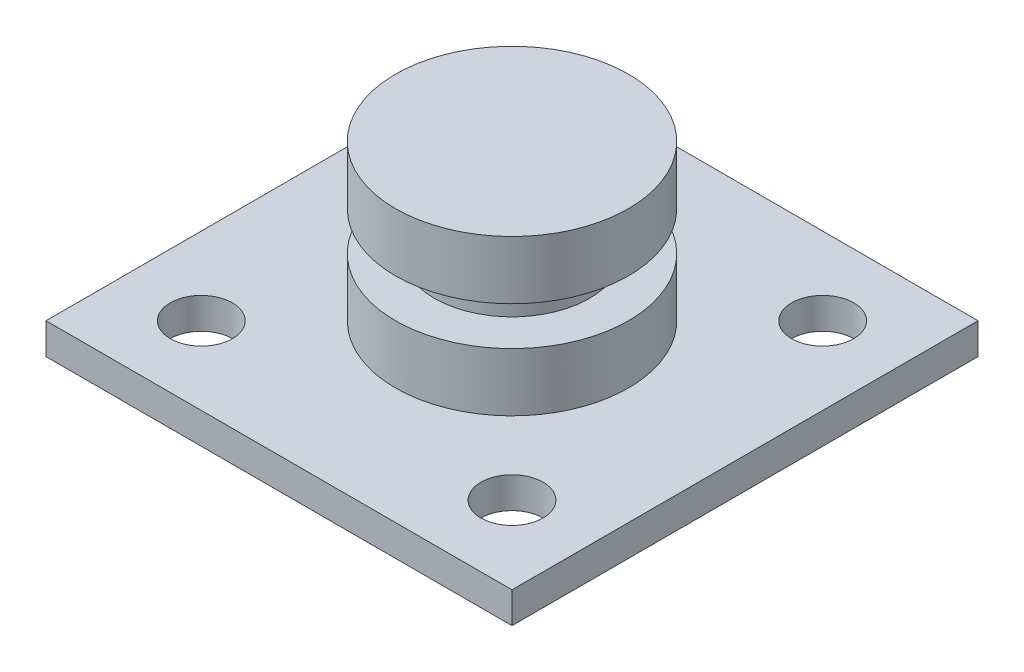
SolidWorks part; units mm, degrees
ref_plane "Front Plane" through (0, 0, 0) normal (0, 0, 1) x (1, 0, 0)
ref_plane "Top Plane" through (0, 0, 0) normal (0, 1, 0) x (1, 0, 0)
ref_plane "Right Plane" through (0, 0, 0) normal (1, 0, 0) x (0, 0, -1)
sketch "Sketch1" plane through (0, 0, 0) normal (0, 1, 0) x (1, 0, 0)
  line L1 (15, -15) -> (-15, -15)
  line L2 (15, -15) -> (15, 15)
  line L3 (15, 15) -> (-15, 15)
  line L4 (-15, -15) -> (-15, 15)
  line L5 (15, -15) -> (-15, 15) construction
  line L6 (15, 15) -> (-15, -15) construction
  point P0 (0, 0)
  dimension "D1" = 30
  dimension "D2" = 30
extrude "Boss-Extrude1" add sketch "Sketch1" along normal blind 2
sketch "Sketch3" plane through (0, 2, 0) normal (0, 1, 0) x (1, 0, 0)
  line L0 (-15, 15) -> (-15, -15) construction
  line L1 (15, 15) -> (-15, 15) construction
  line L2 (-15, -15) -> (15, -15) construction
  circle A0 centre (-10, 10) radius 2
  circle A1 centre (10, 10) radius 2
  circle A2 centre (10, -10) radius 2
  circle A3 centre (-10, -10) radius 2
  dimension "D2" = 5
  dimension "D3" = 5
  dimension "D5" = 5
  dimension "D6" = 5
  dimension "D8" = 4
  dimension "D1" = 20
  dimension "D4" = 20
  dimension "D7" = 5
extrude "Cut-Extrude1" cut sketch "Sketch3" against normal blind 5
sketch "Sketch2" plane through (0, 2, 0) normal (0, 1, 0) x (1, 0, 0)
  circle A0 centre (0, 0) radius 7.5
  dimension "D1" = 15
extrude "Boss-Extrude2" add sketch "Sketch2" along normal blind 10
sketch "Sketch4" plane through (0, 0, 0) normal (1, 0, 0) x (0, 0, -1)
  line L0 (-7.5, 12) -> (-7.5, 2) construction
  line L1 (-5, 5.75) -> (-10, 5.75)
  line L2 (-5, 5.75) -> (-5, 8.25)
  line L3 (-5, 8.25) -> (-10, 8.25)
  line L4 (-10, 5.75) -> (-10, 8.25)
  line L5 (-5, 5.75) -> (-10, 8.25) construction
  line L6 (-5, 8.25) -> (-10, 5.75) construction
  line L7 (0, 16.444) -> (0, -2.4077) construction
  point P0 (-7.5, 7)
  dimension "D1" = 5
  dimension "D2" = 2.5
revolve "Cut-Revolve1" cut sketch "Sketch4" angle 360 about L7
